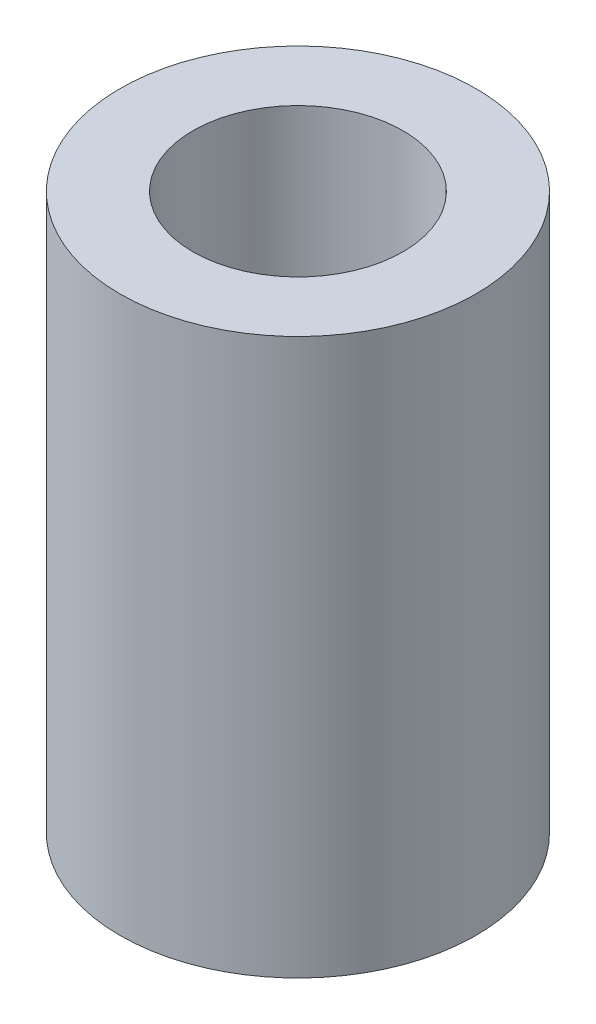
SolidWorks part; units mm, degrees
ref_plane "Front Plane" through (0, 0, 0) normal (0, 0, 1) x (1, 0, 0)
ref_plane "Top Plane" through (0, 0, 0) normal (0, 1, 0) x (1, 0, 0)
ref_plane "Right Plane" through (0, 0, 0) normal (1, 0, 0) x (0, 0, -1)
sketch "Sketch1" plane through (0, 0, 0) normal (0, 1, 0) x (1, 0, 0)
  circle A0 centre (0, 0) radius 3.6
  circle A1 centre (0, 0) radius 6.1
  dimension "D1" = 7.2
  dimension "D2" = 12.2
extrude "Boss-Extrude1" add sketch "Sketch1" along normal blind 19.05
